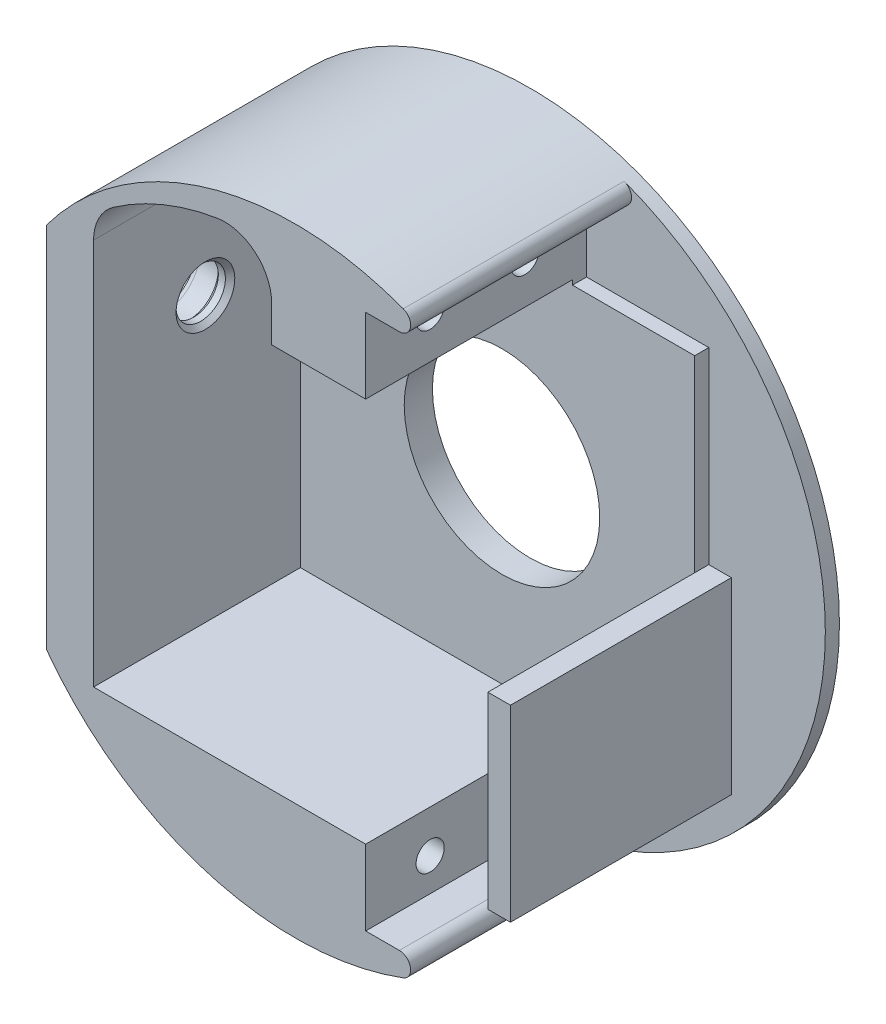
SolidWorks part; units mm, degrees
ref_plane "Front Plane" through (0, 0, 0) normal (0, 0, 1) x (1, 0, 0)
ref_plane "Top Plane" through (0, 0, 0) normal (0, 1, 0) x (1, 0, 0)
ref_plane "Right Plane" through (0, 0, 0) normal (1, 0, 0) x (0, 0, -1)
sketch "Sketch2" plane through (0, 0, 0) normal (0, 0, 1) x (1, 0, 0)
  circle A0 centre (9.62, 10) radius 32.9
  circle A1 centre (9.62, 10) radius 32.9 construction
  circle A2 centre (9.62, 10) radius 10.4
  circle A4 centre (9.62, 10) radius 10.4 construction
extrude "Boss-Extrude1" add sketch "Sketch2" along normal blind 25
sketch "Sketch4" plane through (0, 0, 25) normal (0, 0, 1) x (1, 0, 0)
  line L1 (29.87, -10) -> (19.87, -10) construction
  line L2 (29.87, -10) -> (29.87, 30) construction
  line L3 (29.87, 30) -> (19.87, 30) construction
  line L4 (-10.63, -10) -> (-10.63, 30) construction
  line L5 (29.87, -10) -> (-10.63, 30) construction
  line L6 (29.87, 30) -> (-10.63, -10) construction
  line L7 (17.12, 30) -> (17.12, 37.5) construction
  line L8 (19.87, 30) -> (19.87, 37.5) construction
  line L9 (17.12, 37.5) -> (19.87, 37.5) construction
  line L11 (17.12, -10) -> (17.12, -17.5) construction
  line L12 (19.87, -10) -> (19.87, -17.5) construction
  line L13 (17.12, -17.5) -> (19.87, -17.5) construction
  line L14 (17.12, 30) -> (1.02, 30) construction
  line L15 (17.12, -10) -> (-10.63, -10) construction
  line L16 (-11.8282, -10.5) -> (17.12, -10.5)
  line L17 (17.12, -10.5) -> (17.12, -18.5)
  line L18 (-11.8282, -10.5) -> (-11.8282, 30.6741)
  line L19 (7.12, 34.3393) -> (7.12, 30.5)
  line L20 (17.12, 30.5) -> (17.12, 38.5)
  line L21 (-3.23, 30) -> (1.02, 30) construction
  line L22 (-3.23, 30) -> (-3.23, 37.5) construction
  line L23 (1.02, 30) -> (1.02, 37.5) construction
  line L24 (-3.23, 37.5) -> (1.02, 37.5) construction
  line L25 (-3.23, 30) -> (-10.63, 30) construction
  line L26 (7.12, 30.5) -> (17.12, 30.5)
  line L27 (30.12, -10) -> (32.52, -10)
  line L28 (30.12, -10) -> (30.12, 10)
  line L29 (32.52, -10) -> (32.52, 10)
  line L30 (17.12, -18.5) -> (26.0565, -18.5)
  line L31 (17.12, 38.5) -> (26.0565, 38.5)
  line L32 (30.12, 10) -> (32.52, 10)
  line L33 (-16.8282, -9.5679) -> (-16.8282, 29.5679)
  circle A1 centre (9.62, 10) radius 32.9 construction
  arc A2 (1.2926, 39.2703) -> (-9.6978, 34.7687) centre (5.7454, 12.7326) ccw
  arc A3 (-11.8282, 30.6741) -> (-9.6978, 34.7687) centre (-6.8282, 30.6741) cw
  arc A5 (7.12, 34.3393) -> (1.2926, 39.2703) centre (2.12, 34.3393) ccw
  arc A6 (-16.8282, 29.5679) -> (-16.8282, -9.5679) centre (9.62, 10) ccw
  circle A10 centre (9.62, 10) radius 32.9
  arc A11 (26.0565, -18.5) -> (26.0565, 38.5) centre (9.62, 10) ccw
  point P0 (9.62, 10)
  point P6 (0, 0)
  point P20 (41.1781, 19.6483)
  point P31 (41.32, 10)
  point P35 (1.7208, 39.3233)
  point P39 (0, 0)
  point P44 (-11.8282, 30.6741)
  point P47 (18.495, -17.5)
  dimension "D13" = 5
  dimension "D16" = 5
  dimension "D20" = 1.25
  dimension "D1" = 40
  dimension "D2" = 40.5
  dimension "D3" = 27.75
  dimension "D4" = 2.75
  dimension "D5" = 7.5
  dimension "D6" = 0.5
  dimension "D7" = 1
  dimension "D8" = 1.1982
  dimension "D9" = 7.4
  dimension "D10" = 16.1
  dimension "D11" = 10
  dimension "D12" = 0.5
  dimension "D14" = 2.4
  dimension "D15" = 0.5
  dimension "D17" = 1
  dimension "D18" = 20
  dimension "D19" = 0
extrude "Cut-Extrude1" cut sketch "Sketch4" against normal offset from surface (22 mm away) 3 up to face at (42.52, 10, 0)
sketch "Sketch5" plane through (0, 0, 3) normal (0, 0, 1) x (1, 0, 0)
  line L0 (17.12, 38.5) -> (26.0565, 38.5)
  line L1 (17.12, -18.5) -> (26.0565, -18.5)
  line L2 (-16.8282, -9.5679) -> (-16.8282, 29.5679)
  line L3 (-16.8282, -9.5679) -> (-16.8282, 29.5679)
  line L4 (17.12, 38.5) -> (17.12, 30)
  line L5 (30.12, 10) -> (30.12, 30)
  line L6 (30.12, 30) -> (17.12, 30)
  line L7 (30.12, 10) -> (32.52, 10)
  line L8 (32.52, 10) -> (32.52, -10)
  line L9 (32.52, -10) -> (17.12, -10)
  line L10 (17.12, -10) -> (17.12, -18.5)
  arc A2 (-16.8282, 29.5679) -> (-16.8282, -9.5679) centre (9.62, 10) ccw
  arc A3 (-16.8282, 29.5679) -> (-16.8282, -9.5679) centre (9.62, 10) ccw
  arc A4 (26.0565, -18.5) -> (26.0565, 38.5) centre (9.62, 10) ccw
  arc A5 (26.0565, -18.5) -> (26.0565, 38.5) centre (9.62, 10) ccw
  dimension "D1" = 0
  dimension "D2" = 0
extrude "Cut-Extrude2" cut sketch "Sketch5" against normal offset from surface (1.5 mm away) 1.5 up to face at (42.52, 10, 0)
sketch "Sketch6" plane through (-16.8282, 0, 0) normal (-1, 0, 0) x (0, 0, 1)
  circle A0 centre (13.1, 19.62) radius 3.625
  circle A1 centre (13.1, 19.62) radius 2.875 construction
  dimension "D1" = 7.25
extrude "Cut-Extrude3" cut sketch "Sketch6" against normal blind 3.25 contours A0
fillet "Fillet1" radius 0.75 1 edges at (-16.8282, 19.62, 16.725)
sketch "Sketch7" plane through (-13.5782, 0, 0) normal (-1, 0, 0) x (0, 0, 1)
  circle A3 centre (13.1, 19.62) radius 2.625
  circle A4 centre (13.1, 19.62) radius 2.625
  dimension "D1" = 1
extrude "Cut-Extrude4" cut sketch "Sketch7" against normal up to next
chamfer "Chamfer1" distance 0.5 angle 45 2 edges at (-11.8282, 16.995, 13.1) (-13.5782, 19.62, 15.725)
sketch "Sketch8" plane through (17.12, 0, 0) normal (1, 0, 0) x (0, 0, -1)
  circle A0 centre (-18.14, -15) radius 1.5
  circle A1 centre (-8.06, -15) radius 1.5
  circle A2 centre (-18.14, 35) radius 1.5
  circle A3 centre (-8.06, 35) radius 1.5
  dimension "D1" = 3
extrude "Cut-Extrude5" cut sketch "Sketch8" against normal blind 8.5
fillet "Fillet2" radius 1.2 2 edges at (26.0565, -18.5, 13.25) (26.0565, 38.5, 13.25)
